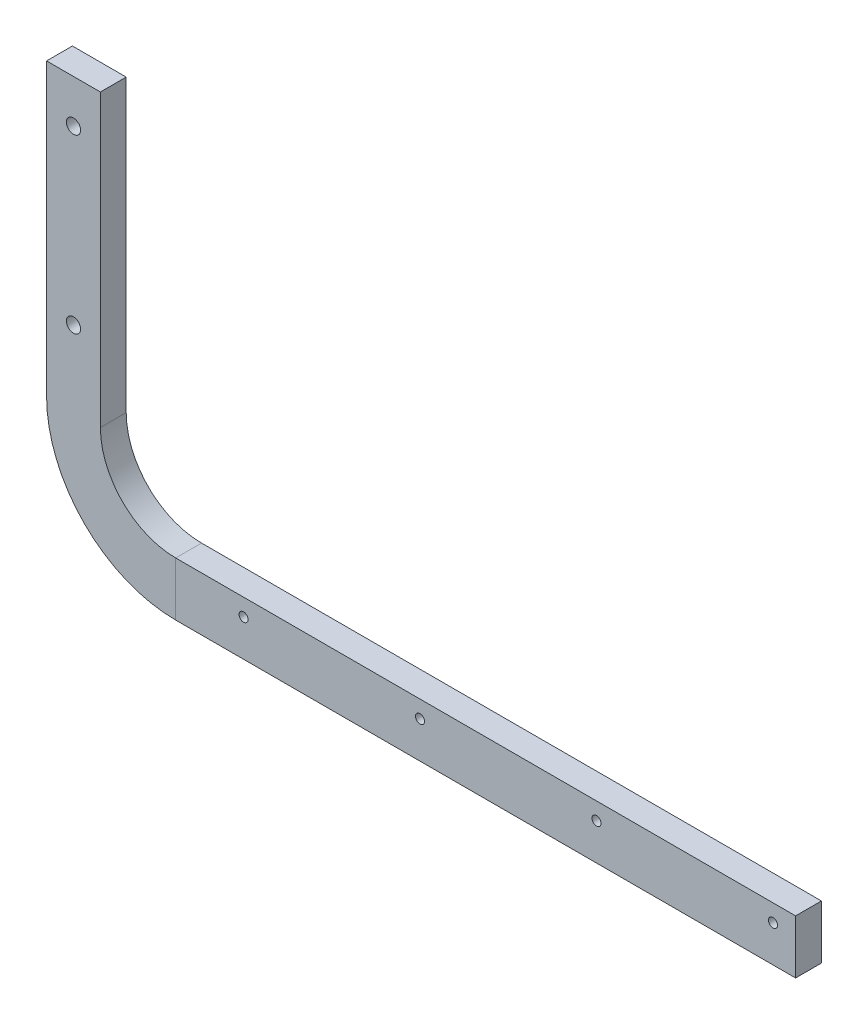
SolidWorks part; units mm, degrees
material "7075-T6, Plate (SS)"
ref_plane "Front Plane" through (0, 0, 0) normal (0, 0, 1) x (1, 0, 0)
ref_plane "Top Plane" through (0, 0, 0) normal (0, 1, 0) x (1, 0, 0)
ref_plane "Right Plane" through (0, 0, 0) normal (1, 0, 0) x (0, 0, -1)
sketch "Sketch1" plane through (0, 0, 0) normal (0, 0, 1) x (1, 0, 0)
  line L0 (0, 0) -> (0, -135)
  line L1 (60, -195) -> (348, -195)
  line L2 (348, -195) -> (348, -170)
  line L3 (348, -170) -> (60, -170)
  line L4 (25, -135) -> (25, 0)
  line L5 (25, 0) -> (0, 0)
  arc A0 (0, -135) -> (60, -195) centre (60, -135) ccw
  arc A1 (60, -170) -> (25, -135) centre (60, -135) cw
  dimension "D5" = 60
  dimension "D6" = 35
  dimension "D1" = 195
  dimension "D2" = 348
  dimension "D3" = 25
  dimension "D4" = 25
extrude "Boss-Extrude1" add sketch "Sketch1" along normal mid plane 12
hole_wizard "M6 Clearance Hole1" positions "Sketch2" profile "Sketch3" hole size "M6" standard "ISO" end condition through all
sketch "Sketch2" plane through (0, 0, 6) normal (0, 0, 1) x (1, 0, 0)
  line L0 (12.5, 0) -> (12.5, -20) construction
  line L1 (25, 0) -> (0, 0) construction
  line L2 (12.5, -20) -> (12.5, -100) construction
  point P0 (12.5, -20)
  point P6 (12.5, -100)
  dimension "D1" = 20
  dimension "D2" = 80
sketch "Sketch3" plane through (12.5, -20, 6) normal (1, 0, 0) x (0, -1, 0)
  line L0 (0, 0) -> (0, 12)
  line L1 (0, 12) -> (3.3, 12)
  line L2 (3.3, 12) -> (3.3, 0)
  line L5 (3.3, 0) -> (0, 0)
  line L11 (0, -6.35) -> (0, 107.95) construction
  dimension "Thru Hole Dia." = 6.6
  dimension "Thru Hole Depth" = 12
sketch "Sketch4" plane through (348, 0, 0) normal (1, 0, 0) x (0, 0, -1)
  line L0 (-6, -195) -> (-6, -170) construction
  line L1 (-6, -176) -> (-1, -176)
  line L2 (-6, -176) -> (-6, -195)
  line L3 (-6, -195) -> (-1, -195)
  line L4 (-1, -176) -> (-1, -195)
  line L5 (-6, -195) -> (6, -195) construction
  line L6 (-6, -170) -> (6, -170) construction
  line L7 (6, -195) -> (6, -170) construction
  dimension "D1" = 6
  dimension "D2" = 7
sketch "Sketch6" plane through (0, -195, 0) normal (0, -1, 0) x (1, 0, 0)
  line L0 (348, 6) -> (78, 6)
  line L1 (60, 6) -> (348, 6) construction
  line L2 (78, 6) -> (78, 38.7665) construction
  dimension "D1" = 270
sweep "Cut-Sweep1" [suppressed] cut profiles "Sketch4" path "Sketch6"
sketch "Sketch7" plane through (0, 0, -6) normal (0, 0, -1) x (-1, 0, 0)
  line L0 (-25, -116.6049) -> (0, -116.6049)
  line L1 (-25, -135) -> (-25, 0) construction
  line L2 (0, 0) -> (0, -135) construction
split line "Split Line1"
sketch "Sketch8" plane through (0, 0, 6) normal (0, 0, 1) x (1, 0, 0)
  line L0 (60, -170) -> (60, -195)
split line "Split Line2"
hole_wizard "M5 Tapped Hole1" positions "Sketch9" profile "Sketch10" tap size "M5" standard "ISO" end condition through all
sketch "Sketch9" plane through (0, 0, 6) normal (0, 0, 1) x (1, 0, 0)
  line L0 (337.5, -175.75) -> (337.5, -180.25) construction
  point P7 (337.5, -178)
sketch "Sketch10" plane through (337.5, -178, 6) normal (1, 0, 0) x (0, -1, 0)
  line L0 (0, 0) -> (0, 12)
  line L1 (0, 12) -> (2.1, 12)
  line L2 (2.1, 12) -> (2.1, 0)
  line L5 (2.1, 0) -> (0, 0)
  line L11 (0, -6.35) -> (0, 107.95) construction
  dimension "Thru Tap Drill Dia." = 4.2
  dimension "Thru Tap Drill Depth" = 12
cosmetic thread "Hole Thread1" parameters "D2"=5
pattern_linear "LPattern1" count 4 spacing 82 along (-1, 0, 0) of "M5 Tapped Hole1"
cosmetic thread "Hole Thread2" parameters "D2"=5
cosmetic thread "Hole Thread3" parameters "D2"=5
cosmetic thread "Hole Thread4" parameters "D2"=5
